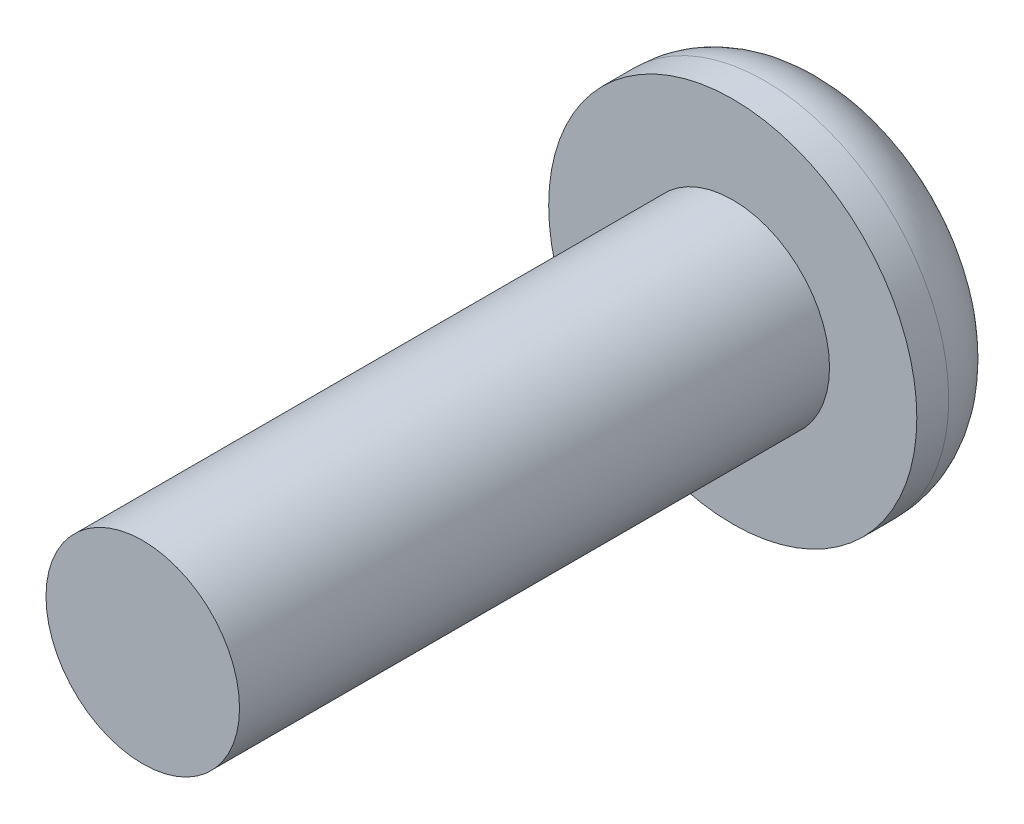
SolidWorks part; units mm, degrees
ref_plane "Front Plane" through (0, 0, 0) normal (0, 0, 1) x (1, 0, 0)
ref_plane "Top Plane" through (0, 0, 0) normal (0, 1, 0) x (1, 0, 0)
ref_plane "Right Plane" through (0, 0, 0) normal (1, 0, 0) x (0, 0, -1)
sketch "Sketch1" plane through (0, 0, 0) normal (0, 0, 1) x (1, 0, 0)
  circle A0 centre (0, 0) radius 3.9624
  dimension "D1" = 7.9248
extrude "Extrude1" add sketch "Sketch1" along normal blind 2.2098
fillet "Fillet1" radius 1.524 1 edges at (3.9624, 0, 0)
sketch "Sketch2" plane through (0, 0, 2.2098) normal (0, 0, 1) x (1, 0, 0)
  circle A0 centre (0, 0) radius 2.0828
  dimension "D1" = 4.1656
extrude "Extrude2" add sketch "Sketch2" along normal blind 12.7
sketch "Sketch3" plane through (0, 0, 0) normal (0, 0, -1) x (-1, 0, 0)
  line L1 (0.709, 1.1779) -> (-0.6656, 1.203)
  line L3 (-0.6656, 1.203) -> (-1.3746, 0.0251)
  line L5 (-1.3746, 0.0251) -> (-0.709, -1.1779)
  line L6 (-0.709, -1.1779) -> (0.6656, -1.203)
  line L7 (0.6656, -1.203) -> (1.3746, -0.0251)
  line L8 (1.3746, -0.0251) -> (0.709, 1.1779)
  circle A1 centre (0, 0) radius 1.1906 construction
  point P0 (0, 0)
  point P8 (0, 0)
  dimension "D1" = 2.3813
extrude "Extrude3" cut sketch "Sketch3" against normal blind 1.016
